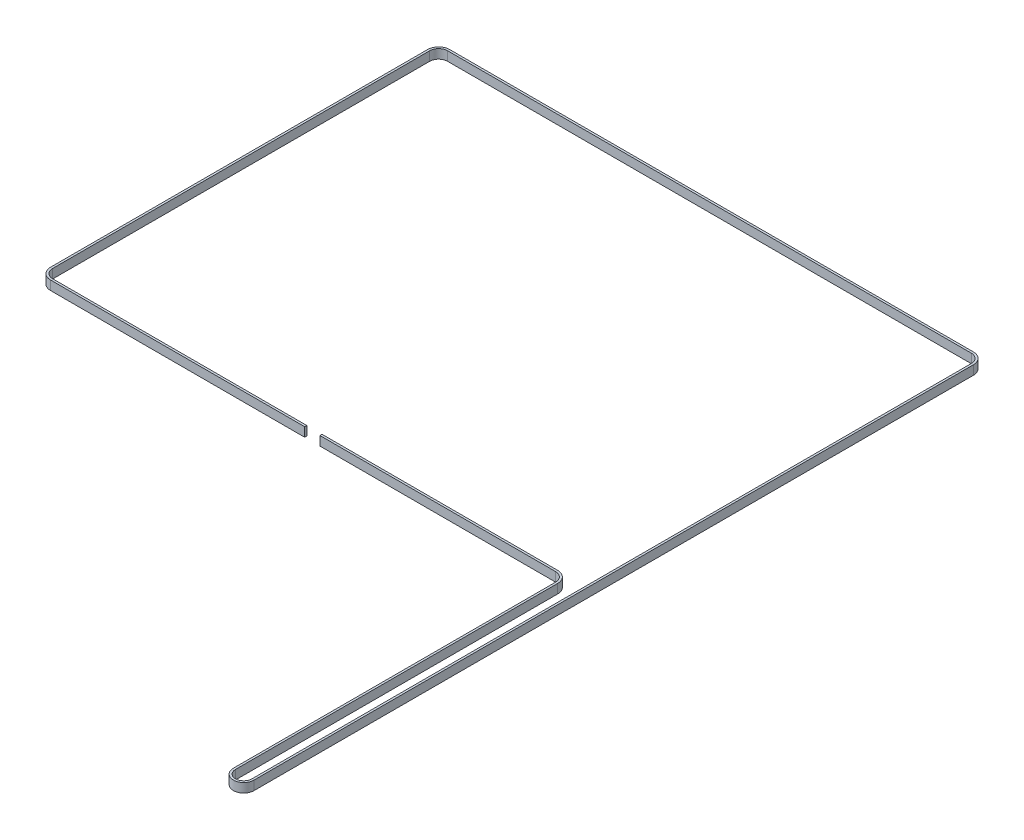
SolidWorks part; units mm, degrees
ref_plane "Front Plane" through (0, 0, 0) normal (0, 0, 1) x (1, 0, 0)
ref_plane "Top Plane" through (0, 0, 0) normal (0, 1, 0) x (1, 0, 0)
ref_plane "Right Plane" through (0, 0, 0) normal (1, 0, 0) x (0, 0, -1)
sketch "Sketch1" plane through (0, 0, 0) normal (0, 1, 0) x (1, 0, 0)
  line L0 (6.875, 0) -> (349.875, 0)
  line L1 (356.75, -6.875) -> (356.75, -478.035)
  line L2 (344.01, -478.035) -> (344.01, -267.0175)
  line L3 (337.64, -260.6475) -> (183.275, -260.6475)
  line L4 (0, -6.875) -> (0, -253.7725)
  line L5 (6.875, -260.6475) -> (173.28, -260.6475)
  arc A0 (356.75, -478.035) -> (344.01, -478.035) centre (350.38, -478.035) cw
  arc A1 (344.01, -267.0175) -> (337.64, -260.6475) centre (337.64, -267.0175) ccw
  arc A2 (349.875, 0) -> (356.75, -6.875) centre (349.875, -6.875) cw
  arc A3 (6.875, 0) -> (0, -6.875) centre (6.875, -6.875) ccw
  arc A4 (0, -253.7725) -> (6.875, -260.6475) centre (6.875, -253.7725) ccw
  point P16 (0, 0)
  dimension "D1" = 6.37
  dimension "D2" = 6.37
  dimension "D5" = 6.875
  dimension "D3" = 343
  dimension "D4" = 471.16
  dimension "D6" = 166.405
  dimension "D7" = 154.365
extrude "Extrude-Thin1" add sketch "Sketch1" along normal blind 6 thin thin type two direction wall 0.376 second wall 1.004
